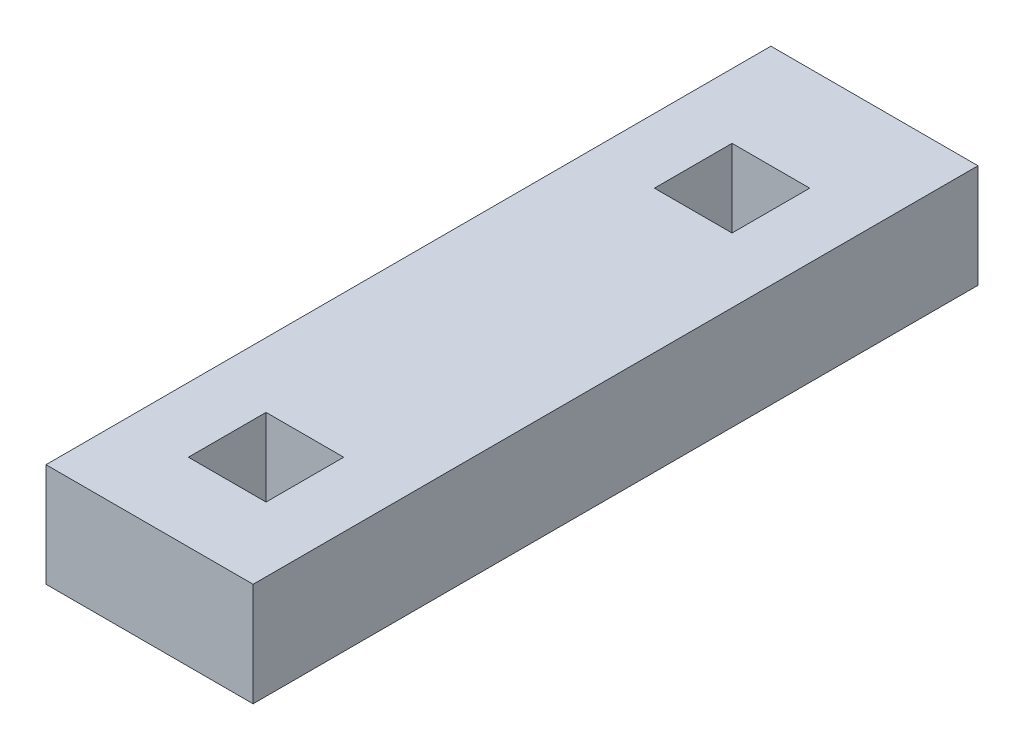
SolidWorks part; units mm, degrees
material "Polyurethane Foam Rigid"
ref_plane "Front Plane" through (0, 0, 0) normal (0, 0, 1) x (1, 0, 0)
ref_plane "Top Plane" through (0, 0, 0) normal (0, 1, 0) x (1, 0, 0)
ref_plane "Right Plane" through (0, 0, 0) normal (1, 0, 0) x (0, 0, -1)
sketch "Sketch1" plane through (0, 0, 0) normal (0, 0, 1) x (1, 0, 0)
  line L1 (0, 0) -> (203.2, 0)
  line L2 (0, 0) -> (0, 101.6)
  line L3 (0, 101.6) -> (203.2, 101.6)
  line L4 (203.2, 0) -> (203.2, 101.6)
  dimension "D1" = 101.6
  dimension "D2" = 203.2
extrude "Boss-Extrude1" add sketch "Sketch1" along normal blind 711.2
sketch "Sketch2" plane through (0, 101.6, 0) normal (0, 1, 0) x (1, 0, 0)
  line L0 (101.6, 0) -> (101.6, -730.0262) construction
  line L1 (203.2, 0) -> (0, 0) construction
  line L2 (203.2, -711.2) -> (0, -711.2) construction
  line L3 (63.5, -177.8) -> (139.7, -177.8)
  line L4 (63.5, -177.8) -> (63.5, -101.6)
  line L5 (63.5, -101.6) -> (139.7, -101.6)
  line L6 (139.7, -177.8) -> (139.7, -101.6)
  line L7 (63.5, -177.8) -> (139.7, -101.6) construction
  line L8 (63.5, -101.6) -> (139.7, -177.8) construction
  line L9 (63.5, -635) -> (139.7, -635)
  line L10 (63.5, -635) -> (63.5, -558.8)
  line L11 (63.5, -558.8) -> (139.7, -558.8)
  line L12 (139.7, -635) -> (139.7, -558.8)
  line L13 (63.5, -635) -> (139.7, -558.8) construction
  line L14 (63.5, -558.8) -> (139.7, -635) construction
  point P4 (101.6, -139.7)
  point P9 (101.6, -596.9)
  dimension "D1" = 76.2
  dimension "D2" = 76.2
  dimension "D3" = 76.2
  dimension "D4" = 76.2
  dimension "D5" = 381
  dimension "D6" = 76.2
extrude "Cut-Extrude1" cut sketch "Sketch2" against normal blind 76.2
